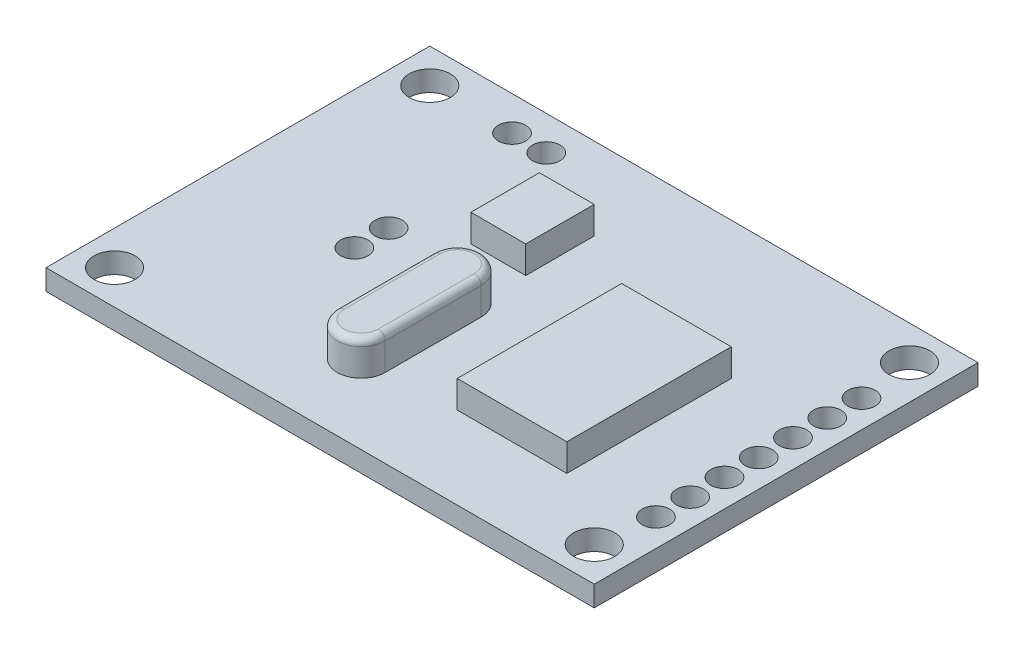
SolidWorks part; units mm, degrees
ref_plane "Front Plane" through (0, 0, 0) normal (0, 0, 1) x (1, 0, 0)
ref_plane "Top Plane" through (0, 0, 0) normal (0, 1, 0) x (1, 0, 0)
ref_plane "Right Plane" through (0, 0, 0) normal (1, 0, 0) x (0, 0, -1)
sketch "Sketch1" plane through (0, 0, 0) normal (0, 1, 0) x (1, 0, 0)
  line L1 (0, 0) -> (40, 0)
  line L2 (0, 0) -> (0, 28)
  line L3 (0, 28) -> (40, 28)
  line L4 (40, 0) -> (40, 28)
  circle A0 centre (2.5, 25.5) radius 1.5
  circle A1 centre (2.5, 2.5) radius 1.5
  circle A2 centre (37.5, 25.5) radius 1.5
  circle A3 centre (37.5, 2.5) radius 1.5
  point P15 (0, 0)
  dimension "D3" = 3
  dimension "D4" = 3
  dimension "D5" = 3
  dimension "D6" = 3
  dimension "D1" = 40
  dimension "D2" = 28
  dimension "D7" = 2.5
  dimension "D8" = 2.5
  dimension "D9" = 2.5
  dimension "D10" = 2.5
  dimension "D11" = 2.5
  dimension "D12" = 2.5
  dimension "D13" = 2.5
  dimension "D14" = 2.5
extrude "Boss-Extrude1" add sketch "Sketch1" along normal blind 1.5
sketch "Sketch2" plane through (0, 1.5, 0) normal (0, 1, 0) x (1, 0, 0)
  line L0 (0, 0) -> (40, 0) construction
  line L1 (40, 0) -> (40, 28) construction
  circle A0 centre (38, 6.5) radius 1
  circle A1 centre (38, 9) radius 1
  circle A2 centre (38, 11.5) radius 1
  circle A3 centre (38, 14) radius 1
  circle A4 centre (38, 16.5) radius 1
  circle A5 centre (38, 19) radius 1
  circle A6 centre (38, 21.5) radius 1
  dimension "D1" = 2
  dimension "D3" = 6.5
  dimension "D4" = 2
  dimension "D2" = 7
extrude "Cut-Extrude1" cut sketch "Sketch2" against normal through all
sketch "Sketch3" plane through (0, 1.5, 0) normal (0, 1, 0) x (1, 0, 0)
  line L0 (0, 0) -> (40, 0) construction
  line L1 (24, 18) -> (32, 18)
  line L2 (24, 18) -> (24, 6)
  line L3 (24, 6) -> (32, 6)
  line L4 (32, 18) -> (32, 6)
  line L5 (40, 0) -> (40, 28) construction
  dimension "D1" = 8
  dimension "D2" = 12
  dimension "D3" = 6
  dimension "D4" = 8
extrude "Boss-Extrude2" add sketch "Sketch3" along normal blind 2
sketch "Sketch4" plane through (0, 1.5, 0) normal (0, 1, 0) x (1, 0, 0)
  line L0 (40, 28) -> (0, 28) construction
  line L1 (14, 22) -> (18, 22)
  line L2 (14, 22) -> (14, 17)
  line L3 (14, 17) -> (18, 17)
  line L4 (18, 22) -> (18, 17)
  line L5 (0, 28) -> (0, 0) construction
  dimension "D1" = 4
  dimension "D2" = 5
  dimension "D3" = 6
  dimension "D4" = 14
extrude "Boss-Extrude3" add sketch "Sketch4" along normal blind 2
sketch "Sketch5" plane through (0, 1.5, 0) normal (0, 1, 0) x (1, 0, 0)
  line L0 (0, 0) -> (40, 0) construction
  line L1 (0, 28) -> (0, 0) construction
  line L3 (40, 28) -> (0, 28) construction
  circle A0 centre (10, 15) radius 1
  circle A1 centre (10, 12.5) radius 1
  circle A2 centre (8.5, 25.5) radius 1
  circle A3 centre (11, 25.5) radius 1
  point P12 (0, 0)
  point P14 (5.16, 28)
  dimension "D1" = 2
  dimension "D2" = 2
  dimension "D6" = 2
  dimension "D7" = 2
  dimension "D3" = 2.5
  dimension "D4" = 12.5
  dimension "D5" = 10
  dimension "D8" = 2.5
  dimension "D9" = 8.5
  dimension "D10" = 2.5
extrude "Cut-Extrude2" cut sketch "Sketch5" against normal through all
sketch "Sketch6" plane through (0, 1.5, 0) normal (0, 1, 0) x (1, 0, 0)
  line L0 (17.25, 12.75) -> (17.25, 5.75) construction
  line L1 (19, 12.75) -> (19, 5.75)
  line L2 (15.5, 12.75) -> (15.5, 5.75)
  line L3 (0, 0) -> (40, 0) construction
  line L4 (0, 28) -> (0, 0) construction
  arc A0 (19, 12.75) -> (15.5, 12.75) centre (17.25, 12.75) ccw
  arc A1 (15.5, 5.75) -> (19, 5.75) centre (17.25, 5.75) ccw
  point P2 (17.25, 9.25)
  point P7 (17.25, 4)
  dimension "D1" = 3.5
  dimension "D2" = 7
  dimension "D3" = 4
  dimension "D4" = 15.5
extrude "Boss-Extrude4" add sketch "Sketch6" along normal blind 2.5
fillet "Fillet1" radius 0.5 4 edges at (17.25, 4, -4) (15.5, 4, -9.25) (17.25, 4, -14.5) (19, 4, -9.25)
